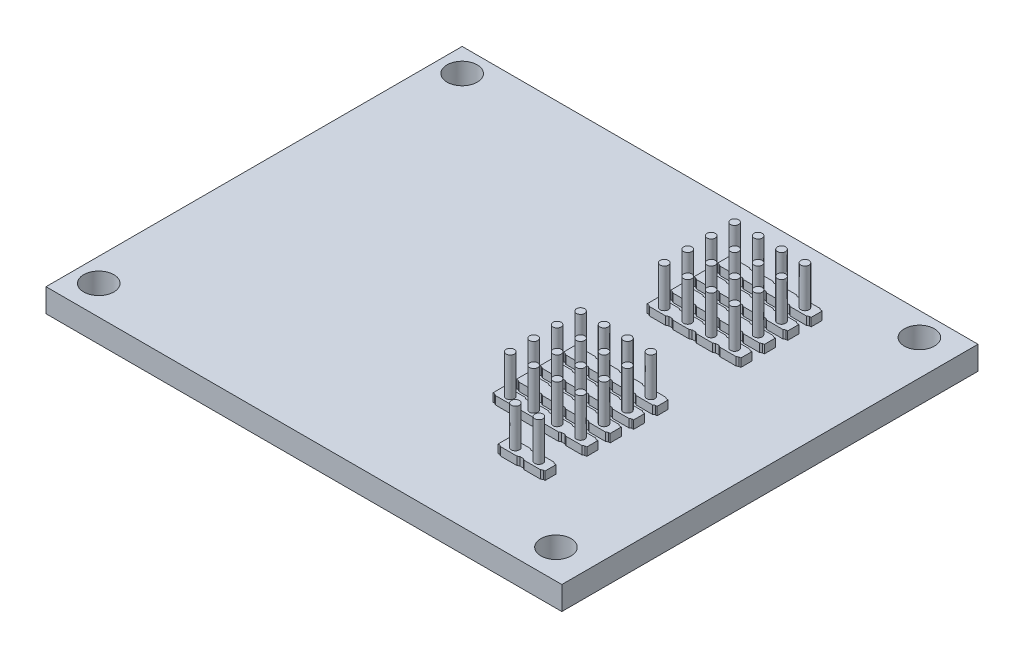
SolidWorks part; units mm, degrees
material "6061-T6 (SS)"
ref_plane "Front Plane" through (0, 0, 0) normal (0, 0, 1) x (1, 0, 0)
ref_plane "Top Plane" through (0, 0, 0) normal (0, 1, 0) x (1, 0, 0)
ref_plane "Right Plane" through (0, 0, 0) normal (1, 0, 0) x (0, 0, -1)
sketch "Sketch1" plane through (0, 0, 0) normal (0, 1, 0) x (1, 0, 0)
  line L1 (-27.94, -22.5425) -> (27.94, -22.5425)
  line L2 (-27.94, -22.5425) -> (-27.94, 22.5425)
  line L3 (-27.94, 22.5425) -> (27.94, 22.5425)
  line L4 (27.94, -22.5425) -> (27.94, 22.5425)
  line L5 (-27.94, -22.5425) -> (27.94, 22.5425) construction
  line L6 (-27.94, 22.5425) -> (27.94, -22.5425) construction
  point P0 (0, 0)
  dimension "D1" = 55.88
  dimension "D2" = 45.085
extrude "Boss-Extrude1" add sketch "Sketch1" along normal blind 2.54
hole_wizard "#4 Clearance Hole1" positions "Sketch2" profile "Sketch3" hole size "#4" standard "ANSI Inch" end condition up to next
sketch "Sketch2" plane through (0, 2.54, 0) normal (0, 1, 0) x (1, 0, 0)
  line L0 (27.94, 22.5425) -> (-27.94, 22.5425) construction
  line L1 (-27.94, 22.5425) -> (-27.94, -22.5425) construction
  point P0 (-25.4, -19.3675)
  point P2 (-25.4, 20.0025)
  point P4 (24.13, 20.0025)
  point P6 (24.13, -19.3675)
  dimension "D1" = 2.54
  dimension "D2" = 2.54
  dimension "D3" = 49.53
  dimension "D4" = 39.37
sketch "Sketch3" plane through (-25.4, 2.54, 19.3675) normal (1, 0, 0) x (0, 0, 1)
  line L0 (0, 0) -> (0, 2.54)
  line L1 (0, 2.54) -> (1.6319, 2.54)
  line L2 (1.6319, 2.54) -> (1.6319, 0)
  line L5 (1.6319, 0) -> (0, 0)
  line L11 (0, -6.35) -> (0, 107.95) construction
  dimension "Thru Hole Dia." = 3.2639
  dimension "Thru Hole Depth" = 2.54
sketch "Sketch4" plane through (0, 2.54, 0) normal (0, 1, 0) x (1, 0, 0)
  line L0 (27.94, 22.5425) -> (-27.94, 22.5425) construction
  line L1 (-27.94, 22.5425) -> (-27.94, -22.5425) construction
  circle A0 centre (16.002, 15.7353) radius 0.4445
  circle A1 centre (16.002, -0.9525) radius 0.4445
  point P8 (0, 0)
  dimension "D1" = 0.889
  dimension "D2" = 6.8072
  dimension "D3" = 43.942
  dimension "D4" = 23.495
extrude "Cut-Extrude1" cut sketch "Sketch4" against normal through all
pattern_linear "LPattern1" count 4 spacing 2.54 along (0, 0, 1) count 4 spacing 2.54 along (-1, 0, 0) of "Cut-Extrude1"
sketch "Sketch5" plane through (0, 2.54, 0) normal (0, 1, 0) x (1, 0, 0)
  circle A0 centre (16.002, -13.0845) radius 0.4445
  circle A1 centre (13.462, -13.0845) radius 0.4445
  circle A2 centre (16.002, -8.5725) radius 0.4445 construction
  point P6 (16.002, -8.5725)
  point P7 (13.462, -8.5725)
  point P9 (0, 0)
  point P11 (0, 0)
  point P12 (0, 0)
  point P13 (16.002, -13.0845)
extrude "Cut-Extrude2" cut sketch "Sketch5" against normal through all
sketch "Sketch6" plane through (0, 2.54, 0) normal (0, 1, 0) x (1, 0, 0)
  line L0 (15.1229, 16.458) -> (14.918, 16.3342)
  line L1 (15.1229, 16.458) -> (16.8811, 16.458)
  line L2 (15.1229, 16.458) -> (15.1229, 15.0126)
  line L3 (15.1229, 15.0126) -> (16.8811, 15.0126)
  line L4 (16.8811, 16.458) -> (16.8811, 15.0126)
  line L5 (15.1229, 16.458) -> (16.8811, 15.0126) construction
  line L6 (15.1229, 15.0126) -> (16.8811, 16.458) construction
  line L7 (14.918, 16.3342) -> (14.732, 16.3342)
  line L8 (14.732, 16.3342) -> (14.732, 15.1364)
  line L9 (14.732, 15.1364) -> (14.918, 15.1364)
  line L10 (14.918, 15.1364) -> (15.1229, 15.0126)
  line L11 (16.002, 15.7353) -> (14.732, 15.7353) construction
  line L12 (16.002, 15.7353) -> (16.002, 15.0126) construction
  line L13 (16.8811, 16.458) -> (17.086, 16.3342)
  line L14 (16.002, 15.7353) -> (13.462, 15.7353) construction
  line L15 (14.732, 15.7353) -> (14.732, 15.1784) construction
  line L16 (17.086, 15.1364) -> (16.8811, 15.0126)
  line L17 (17.272, 15.7353) -> (17.272, 15.1784) construction
  line L18 (17.272, 15.1364) -> (17.086, 15.1364)
  line L19 (17.272, 16.3342) -> (17.272, 15.1364)
  line L20 (17.086, 16.3342) -> (17.272, 16.3342)
  point P0 (16.002, 15.7353)
  point P13 (14.9277, 16.3288)
  point P23 (14.918, 16.3342)
  circle M18 centre (16.002, 15.7353) radius 0.4445
extrude "Boss-Extrude2" add sketch "Sketch6" along normal blind 0.889 contours L20 L13 L4 L16 L18 L19 | L4 L1 L2 L3 M18 | L9 L10 L2 L0 L7 L8
pattern_linear "LPattern3" count 4 spacing 2.54 along (0, 0, 1) count 4 spacing 2.54 along (-1, 0, 0) of "Boss-Extrude2"
pattern_linear "LPattern4" count 2 spacing 16.6878 along (0, 0, 1) of "Boss-Extrude2"
pattern_linear "LPattern5" count 4 spacing 2.54 along (0, 0, 1) count 4 spacing 2.54 along (-1, 0, 0) of "LPattern4"
pattern_linear "LPattern6" count 2 spacing 28.829 along (0, 0, 1) of "Boss-Extrude2"
pattern_linear "LPattern7" count 2 spacing 2.54 along (-1, 0, 0) of "LPattern6"
sketch "Sketch7" plane through (0, 2.54, 0) normal (0, 1, 0) x (1, 0, 0)
  circle A0 centre (16.002, 15.7353) radius 0.4445
  circle A1 centre (16.002, 15.7353) radius 0.4445 construction
  circle A2 centre (13.462, 15.7353) radius 0.4445
  circle A3 centre (10.922, 15.7353) radius 0.4445
  circle A4 centre (8.382, 15.7353) radius 0.4445
  circle A5 centre (8.382, 13.1953) radius 0.4445
  circle A6 centre (10.922, 13.1953) radius 0.4445
  circle A7 centre (13.462, 13.1953) radius 0.4445
  circle A8 centre (16.002, 13.1953) radius 0.4445
  circle A9 centre (16.002, 10.6553) radius 0.4445
  circle A10 centre (13.462, 10.6553) radius 0.4445
  circle A11 centre (10.922, 10.6553) radius 0.4445
  circle A12 centre (8.382, 10.6553) radius 0.4445
  circle A13 centre (8.382, 8.1153) radius 0.4445
  circle A14 centre (10.922, 8.1153) radius 0.4445
  circle A15 centre (13.462, 8.1153) radius 0.4445
  circle A16 centre (16.002, 8.1153) radius 0.4445
  circle A17 centre (16.002, -0.9525) radius 0.4445
  circle A18 centre (16.002, -3.4925) radius 0.4445
  circle A19 centre (16.002, -6.0325) radius 0.4445
  circle A20 centre (16.002, -8.5725) radius 0.4445
  circle A21 centre (13.462, -0.9525) radius 0.4445
  circle A22 centre (13.462, -3.4925) radius 0.4445
  circle A23 centre (13.462, -6.0325) radius 0.4445
  circle A24 centre (13.462, -8.5725) radius 0.4445
  circle A25 centre (10.922, -8.5725) radius 0.4445
  circle A26 centre (10.922, -6.0325) radius 0.4445
  circle A27 centre (10.922, -3.4925) radius 0.4445
  circle A28 centre (10.922, -0.9525) radius 0.4445
  circle A29 centre (8.382, -0.9525) radius 0.4445
  circle A30 centre (8.382, -3.4925) radius 0.4445
  circle A31 centre (8.382, -6.0325) radius 0.4445
  circle A32 centre (8.382, -8.5725) radius 0.4445
  circle A33 centre (16.002, -13.0937) radius 0.4445
  circle A34 centre (13.462, -13.0937) radius 0.4445
extrude "Boss-Extrude3" add sketch "Sketch7" along normal blind 5.08 and the other way blind 5.08
